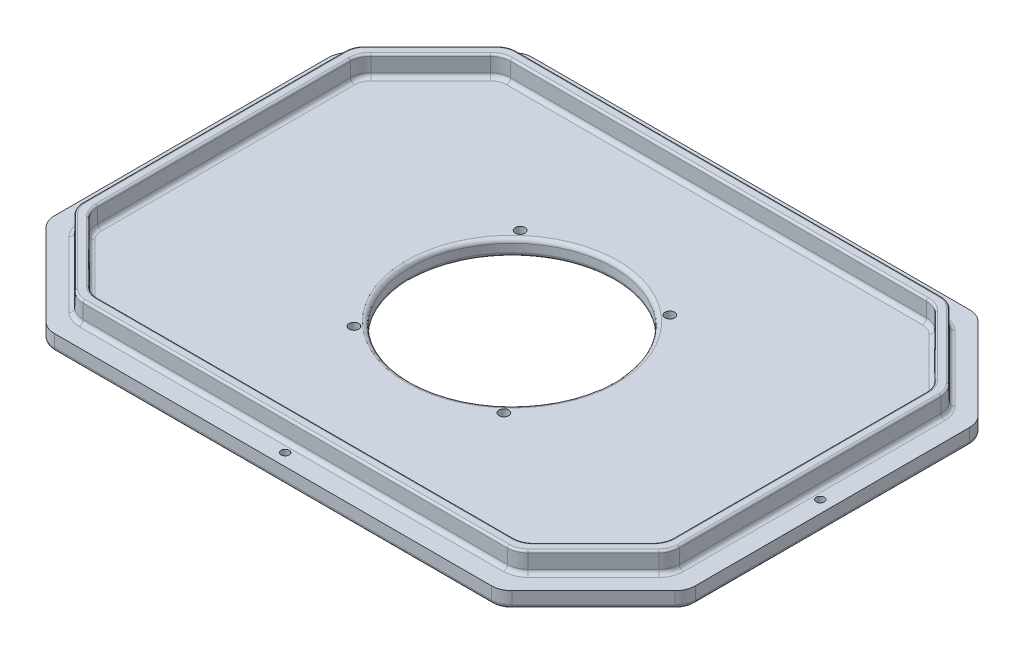
SolidWorks part; units mm, degrees
ref_plane "Front Plane" through (0, 0, 0) normal (0, 0, 1) x (1, 0, 0)
ref_plane "Top Plane" through (0, 0, 0) normal (0, 1, 0) x (1, 0, 0)
ref_plane "Right Plane" through (0, 0, 0) normal (1, 0, 0) x (0, 0, -1)
sketch "Sketch1" plane through (0, 0, 0) normal (0, 1, 0) x (1, 0, 0)
  line L0 (111.5381, -117.5) -> (157.5, -71.5381)
  line L1 (-55, 0) -> (55, 0) construction
  line L2 (-146.5, -68.3959) -> (-146.5, 68.3959)
  line L3 (-146.5, -106.5) -> (-108.3959, -106.5) construction
  line L4 (146.5, -68.3959) -> (146.5, 68.3959)
  line L5 (-146.5, -106.5) -> (146.5, 106.5) construction
  line L6 (-146.5, 106.5) -> (146.5, -106.5) construction
  line L7 (-111.5381, -117.5) -> (111.5381, -117.5)
  line L8 (-157.5, -71.5381) -> (-157.5, 71.5381)
  line L9 (-111.5381, 117.5) -> (111.5381, 117.5)
  line L10 (157.5, -71.5381) -> (157.5, 71.5381)
  line L11 (-157.5, -117.5) -> (157.5, 117.5) construction
  line L12 (-157.5, 117.5) -> (157.5, -117.5) construction
  line L14 (111.5381, -117.5) -> (157.5, -117.5) construction
  line L15 (157.5, -117.5) -> (157.5, -71.5381) construction
  line L16 (146.5, -106.5) -> (146.5, -68.3959) construction
  line L17 (108.3959, 106.5) -> (146.5, 68.3959)
  line L18 (111.5381, 117.5) -> (157.5, 71.5381)
  line L20 (108.3959, -106.5) -> (146.5, -106.5) construction
  line L21 (108.3959, -106.5) -> (146.5, -68.3959)
  line L22 (108.3959, 106.5) -> (146.5, 106.5) construction
  line L29 (111.5381, 117.5) -> (157.5, 117.5) construction
  line L30 (157.5, 71.5381) -> (157.5, 117.5) construction
  line L31 (146.5, 106.5) -> (146.5, 68.3959) construction
  line L32 (0, -55) -> (0, 55) construction
  line L33 (-111.5381, -117.5) -> (-157.5, -71.5381)
  line L34 (-108.3959, -106.5) -> (-146.5, -68.3959)
  line L35 (-111.5381, 117.5) -> (-157.5, 71.5381)
  line L36 (-157.5, 117.5) -> (-111.5381, 117.5) construction
  line L37 (-157.5, 71.5381) -> (-157.5, 117.5) construction
  line L38 (-146.5, 68.3959) -> (-146.5, 106.5) construction
  line L39 (-108.3959, 106.5) -> (-146.5, 68.3959)
  line L40 (-108.3959, 106.5) -> (108.3959, 106.5)
  line L41 (-146.5, 106.5) -> (-108.3959, 106.5) construction
  line L43 (-146.5, -106.5) -> (-146.5, -68.3959) construction
  line L45 (-108.3959, -106.5) -> (108.3959, -106.5)
  line L48 (-157.5, -117.5) -> (-157.5, -71.5381) construction
  line L49 (-157.5, -117.5) -> (-111.5381, -117.5) construction
  line L51 (104.467, -110.4289) -> (150.4289, -64.467) construction
  point P0 (0, 0)
  point P5 (0, 0)
  dimension "D1" = 293
  dimension "D2" = 213
  dimension "D3" = 235
  dimension "D4" = 315
  dimension "D5" = 65
  dimension "D6" = 45
  dimension "D7" = 10
extrude "Boss-Extrude1" add sketch "Sketch1" along normal mid plane 8 contours L34 L45 L21 L4 L17 L40 L39 L2 | L9 L35 L8 L33 L7 L0 L10 L18 L45 L34 L2 L39 L40 L17 L4 L21
sketch "Sketch2" plane through (0, 4, 0) normal (0, 1, 0) x (1, 0, 0)
  line L0 (108.3959, 106.5) -> (146.5, 68.3959) construction
  line L1 (146.5, -68.3959) -> (146.5, 68.3959) construction
  line L2 (108.3959, -106.5) -> (146.5, -68.3959) construction
  line L3 (-108.3959, -106.5) -> (108.3959, -106.5) construction
  line L4 (-108.3959, -106.5) -> (-146.5, -68.3959) construction
  line L5 (-146.5, -68.3959) -> (-146.5, 68.3959) construction
  line L6 (-108.3959, 106.5) -> (108.3959, 106.5) construction
  line L7 (-108.3959, 106.5) -> (-146.5, 68.3959) construction
  line L8 (108.3959, 106.5) -> (146.5, 68.3959)
  line L9 (146.5, -68.3959) -> (146.5, 68.3959)
  line L10 (108.3959, -106.5) -> (146.5, -68.3959)
  line L11 (-108.3959, -106.5) -> (108.3959, -106.5)
  line L12 (-108.3959, -106.5) -> (-146.5, -68.3959)
  line L13 (-146.5, -68.3959) -> (-146.5, 68.3959)
  line L14 (-108.3959, 106.5) -> (108.3959, 106.5)
  line L15 (-108.3959, 106.5) -> (-146.5, 68.3959)
  line L16 (106.3249, 101.5) -> (141.5, 66.3249)
  line L17 (141.5, -66.3249) -> (141.5, 66.3249)
  line L18 (106.3249, -101.5) -> (141.5, -66.3249)
  line L19 (-106.3249, -101.5) -> (106.3249, -101.5)
  line L20 (-106.3249, -101.5) -> (-141.5, -66.3249)
  line L21 (-141.5, -66.3249) -> (-141.5, 66.3249)
  line L22 (-106.3249, 101.5) -> (-141.5, 66.3249)
  line L23 (-106.3249, 101.5) -> (106.3249, 101.5)
  dimension "D1" = 5
extrude "Boss-Extrude2" add sketch "Sketch2" along normal blind 10
sketch "Sketch3" plane through (0, 4, 0) normal (0, 1, 0) x (1, 0, 0)
  line L0 (108.3959, 106.5) -> (-108.3959, 106.5) construction
  line L1 (-108.3959, -106.5) -> (108.3959, -106.5) construction
  line L2 (146.5, -68.3959) -> (146.5, 68.3959) construction
  line L3 (-146.5, 68.3959) -> (-146.5, -68.3959) construction
  circle A0 centre (0, 111.5) radius 2
  circle A1 centre (0, -111.5) radius 2
  circle A2 centre (151.5, 0) radius 2
  circle A3 centre (-151.5, 0) radius 2
  dimension "D1" = 4
  dimension "D2" = 5
  dimension "D3" = 5
  dimension "D4" = 5
  dimension "D5" = 5
extrude "Cut-Extrude1" cut sketch "Sketch3" against normal through all both and the other way through all
sketch "Sketch4" plane through (0, -4, 0) normal (0, -1, 0) x (1, 0, 0)
  circle A0 centre (0, 0) radius 50
  circle A1 centre (36, -41.5812) radius 3 construction
  circle A2 centre (0, 0) radius 55 construction
  circle A3 centre (-36.842, 40.8371) radius 2.4
  circle A4 centre (36.842, 40.8371) radius 2.4
  circle A5 centre (-36.842, -40.8371) radius 2.4
  circle A6 centre (36, -41.5812) radius 2.4
  point P8 (-36.842, -40.8371)
  point P9 (36.842, 40.8371)
  point P10 (-36.842, 40.8371)
  point P11 (36, -41.5812)
  point P19 (36.842, 40.8371)
  point P20 (-36.842, -40.8371)
  point P21 (36, -44.5812)
  dimension "D1" = 100
  dimension "D2" = 110
  dimension "D3" = 6
  dimension "D8" = 4.8
  dimension "D9" = 4.8
  dimension "D4" = 36
  dimension "D5" = 81.6742
  dimension "D6" = 36.842
  dimension "D7" = 36.842
extrude "Cut-Extrude2" cut sketch "Sketch4" against normal through all both contours A5 | A6 | A3 | A4 | A0
fillet "Fillet1" radius 10 24 edges at (108.3959, 9, 106.5) (146.5, 9, 68.3959) (146.5, 9, -68.3959) (108.3959, 9, -106.5) (-108.3959, 9, -106.5) (-146.5, 9, -68.3959) (-146.5, 9, 68.3959) (-108.3959, 9, 106.5) (111.5381, 0, 117.5) (157.5, 0, 71.5381) (-111.5381, 0, 117.5) (-157.5, 0, 71.5381) (-157.5, 0, -71.5381) (-111.5381, 0, -117.5) (157.5, 0, -71.5381) (111.5381, 0, -117.5) (141.5, 9, -66.3249) (106.3249, 9, -101.5) (106.3249, 9, 101.5) (141.5, 9, 66.3249) (-141.5, 9, 66.3249) (-106.3249, 9, 101.5) (-106.3249, 9, -101.5) (-141.5, 9, -66.3249)
fillet "Fillet3" radius 2 32 edges at (106.0096, 4, -100.7388) (123.9124, 4, -83.9124) (140.7388, 4, -66.0096) (141.5, 4, 0) (140.7388, 4, 66.0096) (123.9124, 4, 83.9124) (106.0096, 4, 100.7388) (0, 4, 101.5) (-106.0096, 4, 100.7388) (-123.9124, 4, 83.9124) (-140.7388, 4, 66.0096) (-141.5, 4, 0) (-140.7388, 4, -66.0096) (-123.9124, 4, -83.9124) (-106.0096, 4, -100.7388) (-108.0806, 4, 105.7388) (-127.448, 4, 87.448) (-145.7388, 4, 68.0806) (-146.5, 4, 0) (-145.7388, 4, -68.0806) (-127.448, 4, -87.448) (-108.0806, 4, -105.7388) (0, 4, -106.5) (108.0806, 4, -105.7388) (127.448, 4, -87.448) (145.7388, 4, -68.0806) (146.5, 4, 0) (145.7388, 4, 68.0806) (127.448, 4, 87.448) (108.0806, 4, 105.7388) (0, 4, -101.5) (0, 4, 106.5)
fillet "Fillet4" radius 1 32 edges at (-140.7388, 14, -66.0096) (-141.5, 14, 0) (-140.7388, 14, 66.0096) (-123.9124, 14, 83.9124) (-106.0096, 14, 100.7388) (0, 14, 101.5) (106.0096, 14, 100.7388) (123.9124, 14, 83.9124) (140.7388, 14, 66.0096) (141.5, 14, 0) (140.7388, 14, -66.0096) (123.9124, 14, -83.9124) (106.0096, 14, -100.7388) (0, 14, -101.5) (-106.0096, 14, -100.7388) (-123.9124, 14, -83.9124) (-108.0806, 14, 105.7388) (-127.448, 14, 87.448) (-145.7388, 14, 68.0806) (-146.5, 14, 0) (-145.7388, 14, -68.0806) (-127.448, 14, -87.448) (-108.0806, 14, -105.7388) (0, 14, -106.5) (108.0806, 14, -105.7388) (127.448, 14, -87.448) (145.7388, 14, -68.0806) (146.5, 14, 0) (145.7388, 14, 68.0806) (127.448, 14, 87.448) (108.0806, 14, 105.7388) (0, 14, 106.5)
fillet "Fillet6" radius 2 16 edges at (-111.2228, -4, 116.7388) (0, -4, 117.5) (111.2228, -4, 116.7388) (134.519, -4, 94.519) (156.7388, -4, 71.2228) (157.5, -4, 0) (156.7388, -4, -71.2228) (134.519, -4, -94.519) (111.2228, -4, -116.7388) (0, -4, -117.5) (-111.2228, -4, -116.7388) (-134.519, -4, -94.519) (-156.7388, -4, -71.2228) (-157.5, -4, 0) (-156.7388, -4, 71.2228) (-134.519, -4, 94.519)
fillet "Fillet7" radius 2 2 edges at (0, 4, 50) (0, -4, -50)
sketch "Sketch5" plane through (0, -4, 0) normal (0, -1, 0) x (1, 0, 0)
  line L0 (-157.5, -67.3959) -> (-157.5, 67.3959) construction
  line L1 (0, 82.5412) -> (0, -82.5412) construction
  line L52 (-70, 70) -> (70, 70) construction
  line L53 (-37.5, -93) -> (37.5, -93) construction
  line L55 (-150, -10) -> (-60, -10) construction
  line L56 (150, -10) -> (60, -10) construction
  line L57 (-50, 0) -> (50, 0) construction
  circle A0 centre (0, 0) radius 50 construction
  circle A1 centre (0, 0) radius 60.5 construction
  text T0 "LAM" font "Times New Roman" height 25
  text T1 "RC" font "Times New Roman" height 25
  text T2 "T-WORKS" font "Times New Roman" height 20
  text T3 "2025" font "Times New Roman" height 23
  point P4 (0, 70)
  point P5 (0, 0)
  point P10 (0, 0)
  point P16 (18.3449, 8.2133)
  point P18 (-6.361, -2.9552)
  point P19 (5.8228, 0)
  point P20 (0, 0)
  point P21 (-19.8985, 0)
  point P60 (0, -93)
  dimension "D1" = 121
  dimension "D3" = 93
  dimension "D4" = 10
  dimension "D5" = 90
  dimension "D6" = 7.5
  dimension "D20" = 140
  dimension "D22" = 75
  dimension "65" = 70
extrude "Cut-Extrude3" [suppressed] cut sketch "Sketch5" against normal blind 5
